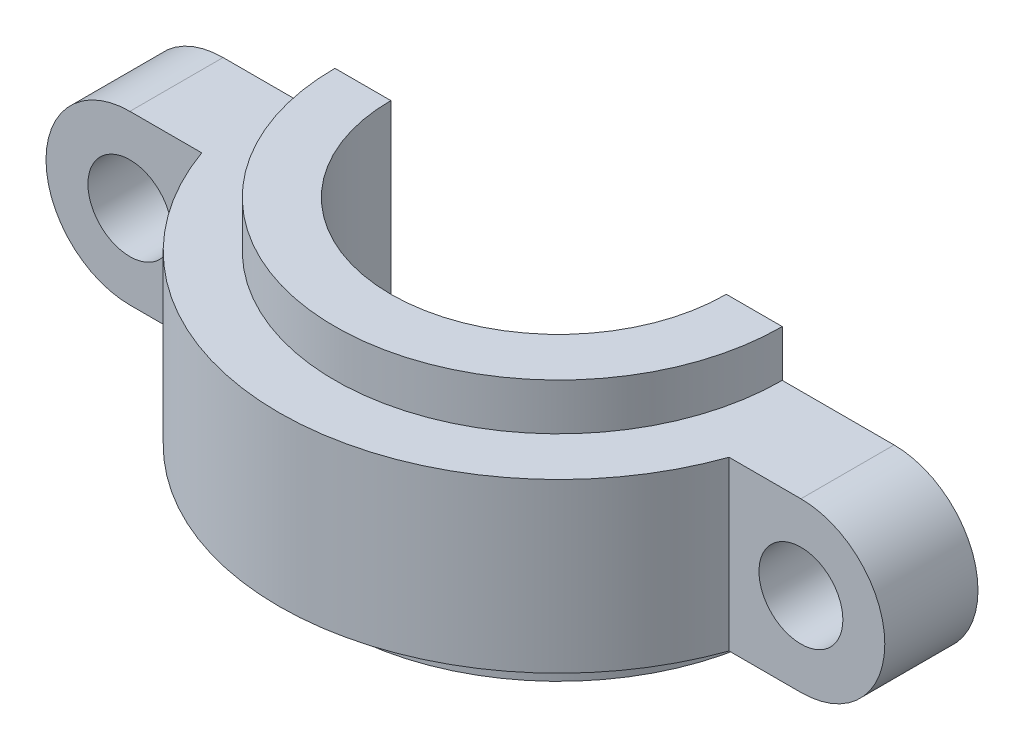
SolidWorks part; units mm, degrees
ref_plane "前基準面" through (0, 0, 0) normal (0, 0, 1) x (1, 0, 0)
ref_plane "上基準面" through (0, 0, 0) normal (0, 1, 0) x (1, 0, 0)
ref_plane "右基準面" through (0, 0, 0) normal (1, 0, 0) x (0, 0, -1)
sketch "草圖1" plane through (0, 0, 0) normal (0, 0, 1) x (1, 0, 0)
  line L7 (0, 38.1636) -> (0, -39.9127) construction
  line L9 (-36, 0) -> (36, 0) construction
  line L10 (-36, 9) -> (36, 9)
  line L11 (-36, -9) -> (36, -9)
  arc A0 (-36, 9) -> (-36, -9) centre (-36, 0) ccw
  arc A1 (36, -9) -> (36, 9) centre (36, 0) ccw
  circle A2 centre (36, 0) radius 4.5
  circle A3 centre (-36, 0) radius 4.5
  point P15 (0, 0)
  dimension "D2" = 9
  dimension "D3" = 9
  dimension "D1" = 72
extrude "填料-伸長1" add sketch "草圖1" along normal blind 10
sketch "草圖3" plane through (0, 0, 0) normal (0, 1, 0) x (1, 0, 0)
  line L0 (0, 20.554) -> (0, -28.709) construction
  line L2 (36, 0) -> (-36, 0) construction
  line L3 (-30, 0) -> (30, 0)
  arc A0 (-30, 0) -> (30, 0) centre (0, 0) ccw
  dimension "D1" = 30
extrude "填料-伸長2" add sketch "草圖3" along normal mid plane 18
sketch "草圖4" plane through (0, 0, 0) normal (0, 1, 0) x (1, 0, 0)
  line L0 (36, 0) -> (-36, 0) construction
  line L1 (-24, 0) -> (24, 0)
  arc A0 (-24, 0) -> (24, 0) centre (0, 0) ccw
  dimension "D1" = 24
extrude "填料-伸長3" add sketch "草圖4" along normal mid plane 28
sketch "草圖5" plane through (0, 14, 0) normal (0, 1, 0) x (1, 0, 0)
  line L0 (24, 0) -> (-24, 0) construction
  line L1 (-18, 0) -> (18, 0)
  arc A0 (-18, 0) -> (18, 0) centre (0, 0) ccw
  dimension "D1" = 18
extrude "除料-伸長1" cut sketch "草圖5" against normal through all
